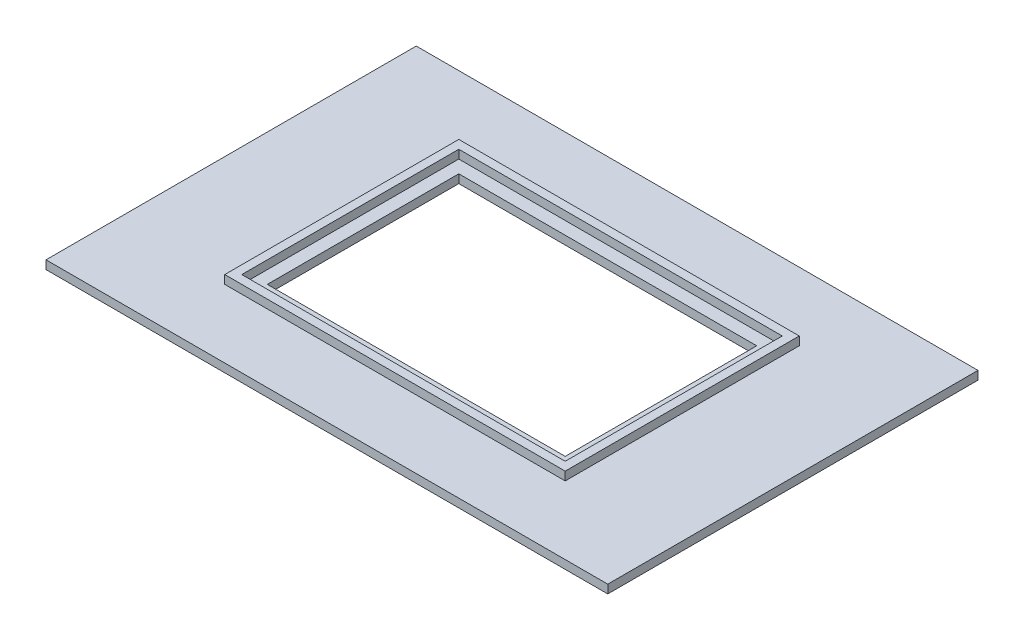
SolidWorks part; units mm, degrees
ref_plane "Front Plane" through (0, 0, 0) normal (0, 0, 1) x (1, 0, 0)
ref_plane "Top Plane" through (0, 0, 0) normal (0, 1, 0) x (1, 0, 0)
ref_plane "Right Plane" through (0, 0, 0) normal (1, 0, 0) x (0, 0, -1)
sketch "Sketch1" plane through (0, 0, 0) normal (0, 1, 0) x (1, 0, 0)
  line L1 (66, -43.5) -> (-66, -43.5)
  line L2 (66, -43.5) -> (66, 43.5)
  line L3 (66, 43.5) -> (-66, 43.5)
  line L4 (-66, -43.5) -> (-66, 43.5)
  line L5 (66, -43.5) -> (-66, 43.5) construction
  line L6 (66, 43.5) -> (-66, -43.5) construction
  point P0 (0, 0)
  dimension "D1" = 132
  dimension "D2" = 87
extrude "Boss-Extrude1" add sketch "Sketch1" along normal blind 2
sketch "Sketch2" plane through (0, 2, 0) normal (0, 1, 0) x (1, 0, 0)
  line L1 (40, -27.5) -> (-40, -27.5)
  line L2 (40, -27.5) -> (40, 27.5)
  line L3 (40, 27.5) -> (-40, 27.5)
  line L4 (-40, -27.5) -> (-40, 27.5)
  line L5 (40, -27.5) -> (-40, 27.5) construction
  line L6 (40, 27.5) -> (-40, -27.5) construction
  point P0 (0, 0)
  dimension "D1" = 80
  dimension "D2" = 55
extrude "Boss-Extrude2" add sketch "Sketch2" along normal blind 2
sketch "Sketch3" plane through (0, 4, 0) normal (0, 1, 0) x (1, 0, 0)
  line L1 (38, -25.5) -> (-38, -25.5)
  line L2 (38, -25.5) -> (38, 25.5)
  line L3 (38, 25.5) -> (-38, 25.5)
  line L4 (-38, -25.5) -> (-38, 25.5)
  line L5 (38, -25.5) -> (-38, 25.5) construction
  line L6 (38, 25.5) -> (-38, -25.5) construction
  point P0 (0, 0)
  dimension "D1" = 76
  dimension "D2" = 51
extrude "Cut-Extrude1" cut sketch "Sketch3" against normal up to surface (2 mm away) up to face at (0, 2, 0)
sketch "Sketch4" plane through (0, 2, 0) normal (0, 1, 0) x (1, 0, 0)
  line L1 (35, -22.5) -> (-35, -22.5)
  line L2 (35, -22.5) -> (35, 22.5)
  line L3 (35, 22.5) -> (-35, 22.5)
  line L4 (-35, -22.5) -> (-35, 22.5)
  line L5 (35, -22.5) -> (-35, 22.5) construction
  line L6 (35, 22.5) -> (-35, -22.5) construction
  point P0 (0, 0)
  dimension "D1" = 70
  dimension "D2" = 45
extrude "Cut-Extrude2" cut sketch "Sketch4" against normal up to surface (2 mm away) up to face at (0, 0, 0)
